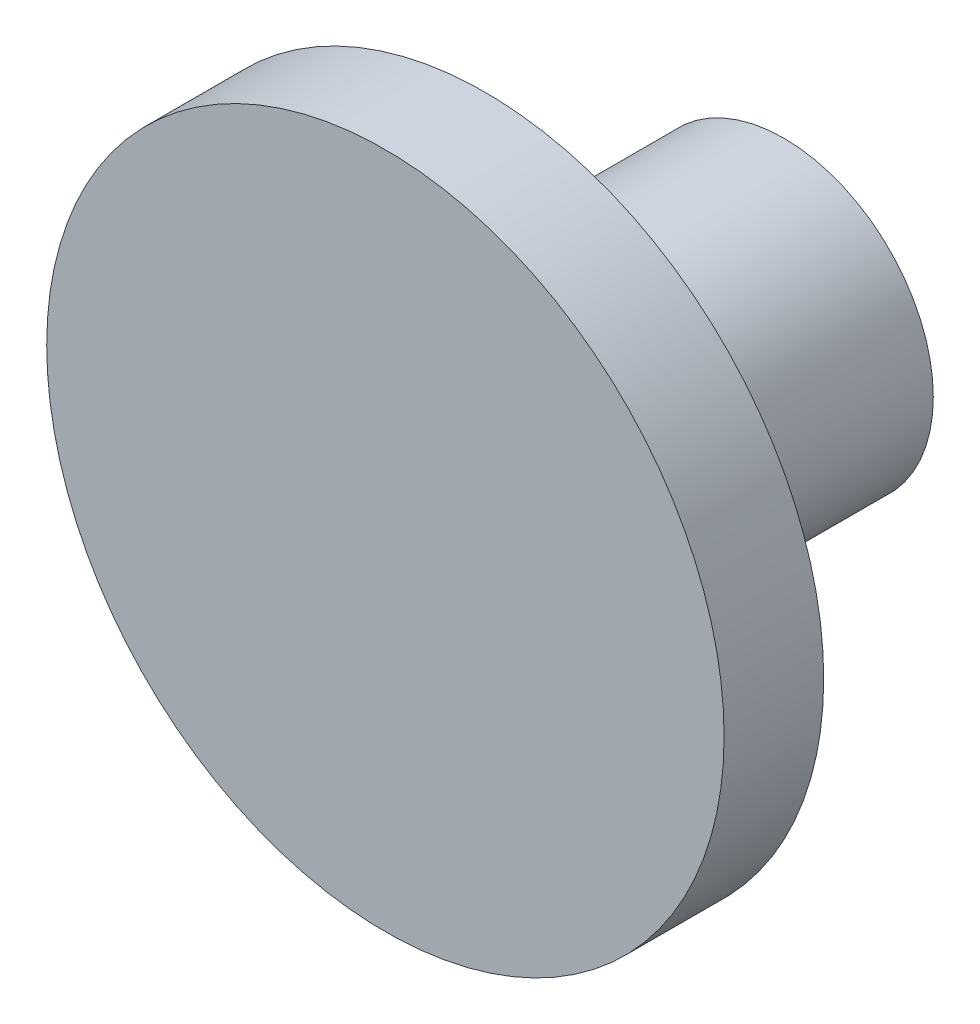
SolidWorks part; units mm, degrees
ref_plane "Plano frontal" through (0, 0, 0) normal (0, 0, 1) x (1, 0, 0)
ref_plane "Plano superior" through (0, 0, 0) normal (0, 1, 0) x (1, 0, 0)
ref_plane "Plano direito" through (0, 0, 0) normal (1, 0, 0) x (0, 0, -1)
sketch "Esboço1" plane through (0, 0, 0) normal (0, 0, 1) x (1, 0, 0)
  circle A0 centre (0, 5) radius 1.5
  dimension "D1" = 3
extrude "Ressalto-extrusão1" add sketch "Esboço1" along normal up to surface (4 mm away)
sketch "Esboço2" plane through (0, 0, 4) normal (0, 0, -1) x (-1, 0, 0)
  circle A0 centre (0, 5) radius 3.4 construction
  circle A1 centre (0, 5) radius 3.4
extrude "Ressalto-extrusão2" add sketch "Esboço2" along normal blind 1
